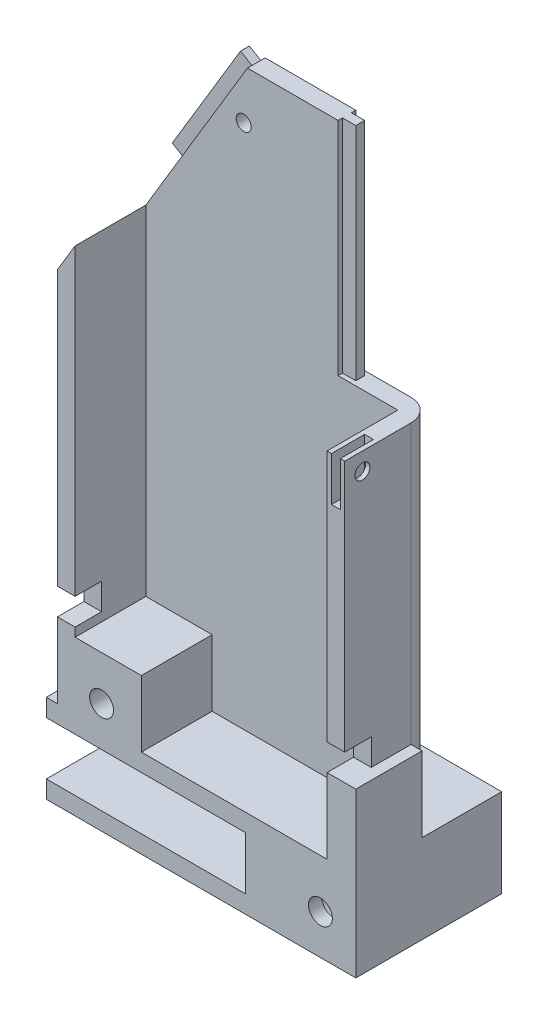
SolidWorks part; units mm, degrees
ref_plane "Front Plane" through (0, 0, 0) normal (0, 0, 1) x (1, 0, 0)
ref_plane "Top Plane" through (0, 0, 0) normal (0, 1, 0) x (1, 0, 0)
ref_plane "Right Plane" through (0, 0, 0) normal (1, 0, 0) x (0, 0, -1)
sketch "Sketch1" plane through (0, 0, 0) normal (0, 1, 0) x (1, 0, 0)
  line L1 (-32.5, -20) -> (32.5, -20)
  line L2 (-32.5, -20) -> (-32.5, 20)
  line L3 (-32.5, 20) -> (32.5, 20)
  line L4 (32.5, -20) -> (32.5, 20)
  line L5 (-32.5, -20) -> (32.5, 20) construction
  line L6 (-32.5, 20) -> (32.5, -20) construction
  point P0 (0, 0)
  dimension "D1" = 65
  dimension "D2" = 40
extrude "Boss-Extrude1" add sketch "Sketch1" along normal blind 130
shell "Shell1" thickness 4
fillet "Fillet1" radius 5 4 edges at (32.5, 65, -20) (32.5, 65, 20) (-32.5, 65, -20) (-32.5, 65, 20)
sketch "Sketch2" plane through (0, 0, 0) normal (0, 0, 1) x (1, 0, 0)
  line L0 (-5.5, 130) -> (-32.5, 85)
  line L1 (28.5, 130) -> (-28.5, 130) construction
  line L2 (-32.5, 130) -> (-32.5, 0) construction
  line L3 (-32.5, 85) -> (-32.5, 130)
  line L4 (-32.5, 130) -> (-5.5, 130)
  dimension "D1" = 5.5
  dimension "D2" = 85
extrude "Cut-Extrude1" cut sketch "Sketch2" against normal through all both and the other way through all
sketch "Sketch3" plane through (0, 0, 0) normal (0, 0, 1) x (1, 0, 0)
  line L1 (32.5, 130) -> (15, 130)
  line L2 (32.5, 130) -> (32.5, 80)
  line L3 (32.5, 80) -> (15, 80)
  line L4 (15, 130) -> (15, 80)
  dimension "D1" = 50
  dimension "D2" = 17.5
extrude "Cut-Extrude2" cut sketch "Sketch3" against normal through all both and the other way through all
sketch "Sketch5" plane through (15, 0, 0) normal (1, 0, 0) x (0, 0, -1)
  line L0 (-18, 130) -> (-18, 80) construction
  line L1 (-16, 130) -> (-20, 130) construction
  line L2 (-16, 80) -> (-20, 80) construction
  line L4 (-19, 130) -> (-17, 130)
  line L5 (-19, 130) -> (-19, 80)
  line L6 (-19, 80) -> (-17, 80)
  line L7 (-17, 130) -> (-17, 80)
  dimension "D1" = 2
extrude "Boss-Extrude2" add sketch "Sketch5" along normal blind 3
mirror "Mirror1" about plane through (0, 0, 0) normal (0, 0, 1) of "Boss-Extrude2"
sketch "Sketch6" plane through (-61.3971, 36.8382, 0) normal (-0.8575, 0.5145, 0) x (0, 0, 1)
  line L0 (-18, 108.6444) -> (-18, 78.6444) construction
  line L1 (-20, 108.6444) -> (-16, 108.6444) construction
  line L3 (-19, 108.6444) -> (-17, 108.6444)
  line L4 (-19, 108.6444) -> (-19, 78.6444)
  line L5 (-19, 78.6444) -> (-17, 78.6444)
  line L6 (-17, 108.6444) -> (-17, 78.6444)
  dimension "D1" = 30
  dimension "D2" = 2
extrude "Boss-Extrude3" add sketch "Sketch6" along normal blind 3
mirror "Mirror2" about plane through (0, 0, 0) normal (0, 0, 1) of "Boss-Extrude3"
sketch "Sketch8" plane through (0, 0, 0) normal (0, 1, 0) x (1, 0, 0)
  line L1 (-35, -33) -> (35, -33)
  line L2 (-35, -33) -> (-35, 33)
  line L3 (-35, 33) -> (35, 33)
  line L4 (35, -33) -> (35, 33)
  line L5 (-35, -33) -> (35, 33) construction
  line L6 (-35, 33) -> (35, -33) construction
  point P0 (0, 0)
  dimension "D1" = 66
  dimension "D2" = 70
extrude "Boss-Extrude4" add sketch "Sketch8" against normal blind 20
sketch "Sketch10" plane through (-35, 0, 0) normal (-1, 0, 0) x (0, 0, 1)
  line L0 (-33, -10) -> (33, -10) construction
  line L1 (-30, -16) -> (30, -16)
  line L2 (-30, -16) -> (-30, -4)
  line L3 (-30, -4) -> (30, -4)
  line L4 (30, -16) -> (30, -4)
  line L5 (-30, -16) -> (30, -4) construction
  line L6 (-30, -4) -> (30, -16) construction
  line L7 (-33, -20) -> (-33, 0) construction
  line L8 (33, -20) -> (33, 0) construction
  line L9 (0, 0) -> (0, -20) construction
  line L10 (-33, -20) -> (33, -20) construction
  point P0 (0, -10)
  dimension "D1" = 60
  dimension "D2" = 12
extrude "Cut-Extrude4" cut sketch "Sketch10" against normal blind 45
sketch "Sketch23" plane through (0, 80, 0) normal (0, 1, 0) x (1, 0, 0)
  line L0 (0, 0) -> (32.5, 0) construction
  line L1 (29.5, 7.5) -> (31.5, 7.5)
  line L2 (29.5, 7.5) -> (29.5, -7.5)
  line L3 (29.5, -7.5) -> (31.5, -7.5)
  line L4 (31.5, 7.5) -> (31.5, -7.5)
  line L5 (32.5, 15) -> (32.5, -15) construction
  line L6 (28.5, 16) -> (28.5, -16) construction
  line L8 (30.5, 14.75) -> (30.5, -14.75) construction
  dimension "D1" = 2
  dimension "D2" = 15
extrude "Cut-Extrude10" cut sketch "Sketch23" against normal blind 10
sketch "Sketch27" plane through (0, 0, 0) normal (0, 1, 0) x (1, 0, 0)
  line L0 (35, -33) -> (35, 33) construction
  line L1 (-35, -33) -> (35, -33)
  line L2 (-35, -33) -> (-35, 0)
  line L3 (-35, 0) -> (35, 0)
  line L4 (35, -33) -> (35, 0)
extrude "Cut-Extrude12" cut sketch "Sketch27" against normal through all both and the other way through all
sketch "Sketch31" plane through (0, 0, 0) normal (0, 0, 1) x (1, 0, 0)
  line L0 (35, -20) -> (35, 0) construction
  line L1 (35, -20) -> (-35, -20) construction
  circle A0 centre (27, -11) radius 2.7
  dimension "D1" = 5.4
  dimension "D2" = 8
  dimension "D3" = 9
extrude "Cut-Extrude15" cut sketch "Sketch31" against normal through all both and the other way through all
sketch "Sketch33" plane through (0, 0, -33) normal (0, 0, -1) x (-1, 0, 0)
  circle A0 centre (-27, -11) radius 4.5
  dimension "D1" = 9
extrude "Cut-Extrude16" cut sketch "Sketch33" against normal blind 30
sketch "Sketch34" plane through (0, 0, 0) normal (0, 1, 0) x (1, 0, 0)
  line L1 (35, 0) -> (35, 33) construction
  line L2 (35, 33) -> (-35, 33) construction
  circle A0 centre (0, 27) radius 1.7
  dimension "D2" = 3.4
  dimension "D1" = 6
  dimension "D3" = 35
extrude "Cut-Extrude17" cut sketch "Sketch34" against normal through all both and the other way through all
sketch "Sketch35" plane through (0, -20, 0) normal (0, -1, 0) x (-1, 0, 0)
  circle A0 centre (0, 27) radius 4
  dimension "D1" = 8
extrude "Cut-Extrude18" cut sketch "Sketch35" against normal blind 2
sketch "Sketch41" plane through (32.5, 0, 0) normal (1, 0, 0) x (0, 0, -1)
  line L0 (0, 80) -> (0, 0) construction
  line L1 (6, 17) -> (0, 17)
  line L2 (6, 17) -> (6, 23)
  line L3 (6, 23) -> (0, 23)
  line L4 (0, 17) -> (0, 23)
  line L5 (0, 0) -> (15, 0) construction
  dimension "D1" = 17
  dimension "D2" = 6
  dimension "D3" = 6
extrude "Cut-Extrude21" cut sketch "Sketch41" against normal through all both and the other way through all
sketch "Sketch42" plane through (32.5, 0, 0) normal (1, 0, 0) x (0, 0, -1)
  line L1 (0, 17) -> (15, 17)
  line L2 (0, 17) -> (0, 0)
  line L3 (0, 0) -> (15, 0)
  line L4 (15, 17) -> (15, 0)
extrude "Boss-Extrude10" add sketch "Sketch42" along normal up to surface (2.5 mm away) up to face at (35, -10, -16.5)
sketch "Sketch43" plane through (32.5, 0, 0) normal (1, 0, 0) x (0, 0, -1)
  line L0 (0, 80) -> (0, 23) construction
  line L1 (15, 80) -> (0, 80) construction
  circle A0 centre (4, 76) radius 1.7
  dimension "D3" = 3.4
  dimension "D1" = 4
  dimension "D2" = 4
extrude "Cut-Extrude22" cut sketch "Sketch43" against normal blind 10 and the other way through all
sketch "Sketch45" plane through (0, 0, -33) normal (0, 0, -1) x (-1, 0, 0)
  line L0 (35, -10) -> (-35, -10) construction
  line L1 (35, -20) -> (35, 0) construction
  line L2 (-35, -20) -> (-35, 0) construction
  line L3 (-35, -20) -> (35, -20) construction
  line L4 (29.4, -16) -> (24.8, -16)
  line L5 (29.4, -16) -> (29.4, -20)
  line L6 (29.4, -20) -> (24.8, -20)
  line L7 (24.8, -16) -> (24.8, -20)
  dimension "D1" = 5.6
  dimension "D2" = 4.6
  dimension "D3" = 4
extrude "Boss-Extrude11" add sketch "Sketch45" along normal blind 3
sketch "Sketch46" plane through (0, -16, 0) normal (0, 1, 0) x (1, 0, 0)
  line L0 (-29.4, 33) -> (-24.8, 36)
  line L1 (-24.8, 36) -> (-29.4, 36)
  line L2 (-29.4, 36) -> (-29.4, 33)
extrude "Cut-Extrude23" cut sketch "Sketch46" against normal through all
fillet "Fillet2" radius 1 1 edges at (-24.8, -18, -36)
sketch "Sketch49" plane through (0, 0, -20) normal (0, 0, -1) x (-1, 0, 0)
  line L0 (6.3575, 118.8526) -> (10.645, 121.4251) construction
  line L1 (5.5, 130) -> (20.9349, 104.2752) construction
  circle A0 centre (6.3575, 118.8526) radius 1.7
  dimension "D1" = 3.4
  dimension "D4" = 5
  dimension "D2" = 5
  dimension "D3" = 10
extrude "Cut-Extrude24" cut sketch "Sketch49" against normal through all both and the other way through all
sketch "Sketch50" plane through (0, 0, -16) normal (0, 0, 1) x (1, 0, 0)
  line L1 (-28.5, 0) -> (-13.5, 0)
  line L2 (-28.5, 0) -> (-28.5, 15)
  line L3 (-28.5, 15) -> (-13.5, 15)
  line L4 (-13.5, 0) -> (-13.5, 15)
  dimension "D1" = 15
  dimension "D2" = 15
extrude "Boss-Extrude12" add sketch "Sketch50" along normal up to vertex (16 mm away)
sketch "Sketch52" plane through (0, 0, -20) normal (0, 0, -1) x (-1, 0, 0)
  line L0 (-27.5, 0) -> (27.5, 0) construction
  line L1 (27.5, 0) -> (27.5, 93.3333) construction
  circle A0 centre (22.5, 5) radius 4.2
  point P2 (0, 0)
  dimension "D1" = 8.4
  dimension "D2" = 5
  dimension "D3" = 5
extrude "Cut-Extrude25" cut sketch "Sketch52" against normal blind 15
sketch "Sketch53" plane through (0, 0, -5) normal (0, 0, -1) x (-1, 0, 0)
  circle A0 centre (22.5, 5) radius 2.7
  dimension "D1" = 5.4
extrude "Cut-Extrude26" cut sketch "Sketch53" against normal through all both and the other way through all
